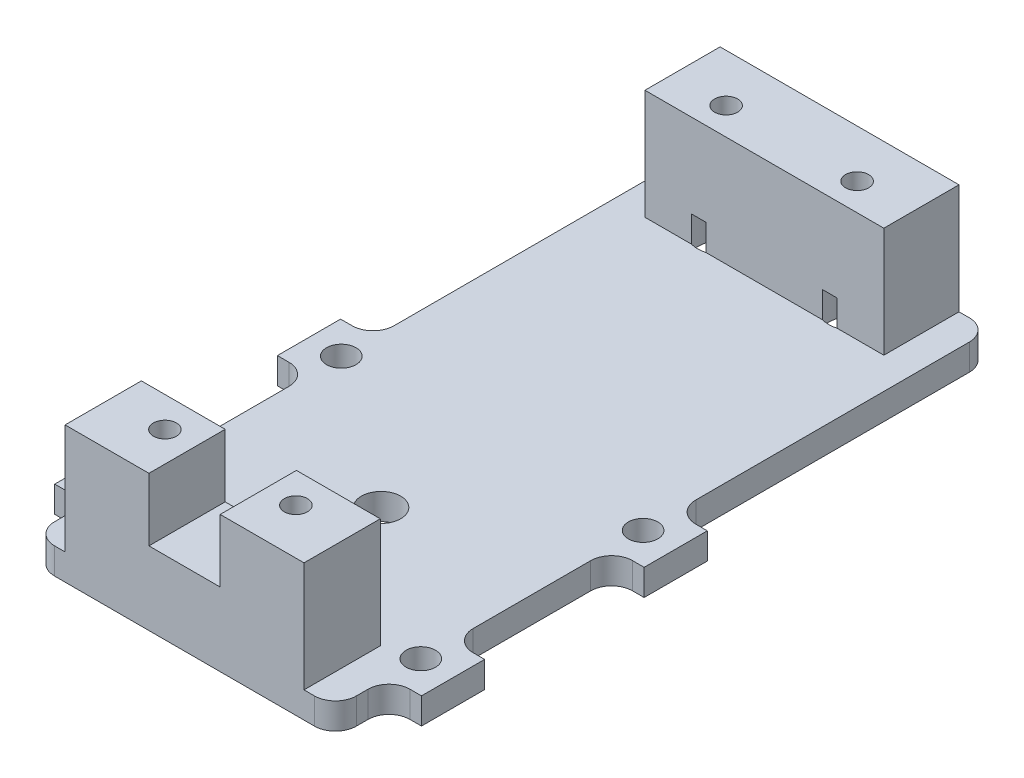
SolidWorks part; units mm, degrees
material "ABS"
ref_plane "Front Plane" through (0, 0, 0) normal (0, 0, 1) x (1, 0, 0)
ref_plane "Top Plane" through (0, 0, 0) normal (0, 1, 0) x (1, 0, 0)
ref_plane "Right Plane" through (0, 0, 0) normal (1, 0, 0) x (0, 0, -1)
sketch "Sketch1" plane through (0, 0, 0) normal (0, 1, 0) x (1, 0, 0)
  line L0 (18.288, -9.6647) -> (22.225, -9.6647)
  line L1 (-18.288, -23.8125) -> (18.288, -23.8125)
  line L2 (-18.288, -23.8125) -> (-18.288, -17.3228)
  line L3 (-18.288, 55.5625) -> (18.288, 55.5625)
  line L4 (18.288, -23.8125) -> (18.288, -17.3228)
  line L5 (-22.225, -17.3228) -> (-18.288, -17.3228)
  line L6 (-22.225, -17.3228) -> (-22.225, -9.6647)
  line L7 (-22.225, 17.3228) -> (-18.288, 17.3228)
  line L8 (22.225, -17.3228) -> (22.225, -9.6647)
  line L9 (0, 0.0043) -> (-31.7584, 0.0043) construction
  line L10 (-31.7584, 0.0043) -> (-18.288, -13.4661) construction
  line L11 (-22.225, -9.6647) -> (-18.288, -9.6647)
  line L12 (-18.288, 17.3228) -> (-18.288, 55.5625)
  line L13 (-22.225, 9.6647) -> (-18.288, 9.6647)
  line L14 (-18.288, -9.6647) -> (-18.288, 9.6647)
  line L15 (18.288, 9.6647) -> (22.225, 9.6647)
  line L17 (18.288, -9.6647) -> (18.288, 9.6647)
  line L18 (22.225, 9.6647) -> (22.225, 17.3228)
  line L19 (-22.225, 9.6647) -> (-22.225, 17.3228)
  line L20 (-18.288, -9.6647) -> (-18.288, 9.6647)
  line L21 (18.288, -9.6647) -> (18.288, 9.6647)
  line L22 (18.288, 17.3228) -> (18.288, 55.5625)
  line L23 (18.288, 17.3228) -> (22.225, 17.3228)
  line L24 (18.288, -17.3228) -> (22.225, -17.3228)
  line L25 (-31.7584, 0.0043) -> (-18.288, 13.4747) construction
  line L26 (0, -23.8125) -> (0, 0.0043) construction
  line L28 (-14.478, -13.8906) -> (14.478, -13.8906) construction
  line L29 (-14.478, -13.8906) -> (-14.478, 45.7994) construction
  line L30 (-14.478, 45.7994) -> (14.478, 45.7994) construction
  line L31 (14.478, -13.8906) -> (14.478, 45.7994) construction
  circle A0 centre (0, 0.0043) radius 2.3812
  circle A1 centre (7.9375, 49.7649) radius 3.429 construction
  circle A2 centre (-7.9375, 49.7649) radius 3.429 construction
  circle A3 centre (7.9375, -18.2563) radius 3.429 construction
  circle A4 centre (-7.9375, -18.2563) radius 3.429 construction
  point P4 (-7.9375, -18.2562)
  point P6 (0, 0)
  point P9 (7.9375, -18.2562)
  point P10 (-7.9375, 49.7649)
  point P11 (7.9375, 49.7649)
  point P31 (18.288, -13.4661)
  point P32 (18.288, 13.4747)
  dimension "D21" = 6.858
  dimension "D1" = 36.576
  dimension "D2" = 79.375
  dimension "D3" = 18.288
  dimension "D4" = 23.8125
  dimension "D5" = 18.2562
  dimension "D6" = 7.9375
  dimension "D9" = 5.5563
  dimension "D10" = 34.6456
  dimension "D11" = 44.45
  dimension "D12" = 19.3294
  dimension "D13" = 9.6647
  dimension "D14" = 19.05
  dimension "D15" = 19.05
  dimension "D16" = 90
  dimension "D17" = 28.956
  dimension "D18" = 14.478
  dimension "D19" = 59.69
  dimension "D20" = 13.8906
  dimension "D7" = 2
  dimension "D8" = 2
extrude "Boss-Extrude1" add sketch "Sketch1" along normal blind 3.175 contours L4 L24 L8 L0 L17 L15 L18 L23 L22 L3 L12 L7 L19 L13 L14 L11 L6 L5 L2 L1 L31 L28 L29 L30
hole_wizard "9/64 (0.14063) Diameter Hole1" positions "Sketch5" profile "Sketch6" hole size "9/64" standard "Ansi Inch" end condition up to next
sketch "Sketch5" plane through (0, 0, 0) normal (0, -1, 0) x (1, 0, 0)
  point P4 (18.288, -13.4747)
  point P7 (18.288, 13.4661)
  point P35 (-18.288, -13.4704)
  point P37 (-18.288, 13.4704)
sketch "Sketch6" plane through (18.288, 0, -13.4747) normal (1, 0, 0) x (0, 0, -1)
  line L0 (0, 0) -> (0, 3.175)
  line L1 (0, 3.175) -> (1.786, 3.175)
  line L2 (1.786, 3.175) -> (1.786, 0)
  line L5 (1.786, 0) -> (0, 0)
  line L11 (0, -6.35) -> (0, 107.95) construction
  dimension "Thru Hole Dia." = 3.572
  dimension "Thru Hole Depth" = 3.175
fillet "Fillet1" radius 2.54 12 edges at (18.288, 1.5875, 23.8125) (18.288, 1.5875, 17.3228) (18.288, 1.5875, 9.6647) (18.288, 1.5875, -9.6647) (18.288, 1.5875, -17.3228) (18.288, 1.5875, -55.5625) (-18.288, 1.5875, -55.5625) (-18.288, 1.5875, -17.3228) (-18.288, 1.5875, -9.6647) (-18.288, 1.5875, 9.6647) (-18.288, 1.5875, 17.3228) (-18.288, 1.5875, 23.8125)
sketch "Sketch9" plane through (0, 0, 0) normal (0, 1, 0) x (1, 0, 0)
  line L0 (-18.288, 55.5625) -> (18.288, 55.5625) construction
  line L1 (-18.288, -23.8125) -> (18.288, -23.8125) construction
  line L5 (-14.478, -14.5696) -> (14.478, -14.5696)
  line L6 (-14.478, -14.5696) -> (-14.478, -23.8125)
  line L8 (-14.4653, 46.453) -> (14.4907, 46.453)
  line L9 (-14.4653, 46.453) -> (-14.4653, 55.5625)
  line L10 (-14.4653, 55.5625) -> (14.4907, 55.5625)
  line L11 (14.4907, 46.453) -> (14.4907, 55.5625)
  line L12 (-14.478, -23.8125) -> (14.478, -23.8125)
  line L13 (14.478, -14.5696) -> (14.478, -23.8125)
  circle A2 centre (-7.9375, -18.2562) radius 1.397
  circle A3 centre (7.9375, -18.2562) radius 1.397
  circle A4 centre (-7.9375, 49.7649) radius 1.397
  circle A5 centre (7.9375, 49.7649) radius 1.397
  dimension "D1" = 2.794
  dimension "D2" = 2.794
  dimension "D3" = 2.794
  dimension "D4" = 2.794
  dimension "D5" = 9.1095
  dimension "D7" = 28.956
  dimension "D8" = 9.2429
extrude "Boss-Extrude3" add sketch "Sketch9" along normal blind 16.51
sketch "Sketch10" plane through (0, 0, 0) normal (0, -1, 0) x (1, 0, 0)
  circle A0 centre (7.9375, 18.2562) radius 3.429
  circle A1 centre (-7.9375, 18.2562) radius 3.429
  circle A2 centre (7.9375, -49.7649) radius 3.429
  circle A3 centre (-7.9375, -49.7649) radius 3.429
extrude "Cut-Extrude1" cut sketch "Sketch10" against normal blind 6.35
sketch "Sketch11" plane through (0, 16.51, 0) normal (0, 1, 0) x (1, 0, 0)
  line L1 (-4.318, -14.5696) -> (4.318, -14.5696)
  line L2 (-4.318, -14.5696) -> (-4.318, -23.8125)
  line L3 (-4.318, -23.8125) -> (4.318, -23.8125)
  line L4 (4.318, -14.5696) -> (4.318, -23.8125)
  line L5 (-14.478, -14.5696) -> (-14.478, -23.8125) construction
  line L6 (14.478, -23.8125) -> (14.478, -14.5696) construction
  point P7 (-14.478, -19.191)
  dimension "D1" = 8.636
  dimension "D2" = 10.16
  dimension "D3" = 10.16
extrude "Cut-Extrude2" cut sketch "Sketch11" against normal blind 7.62
